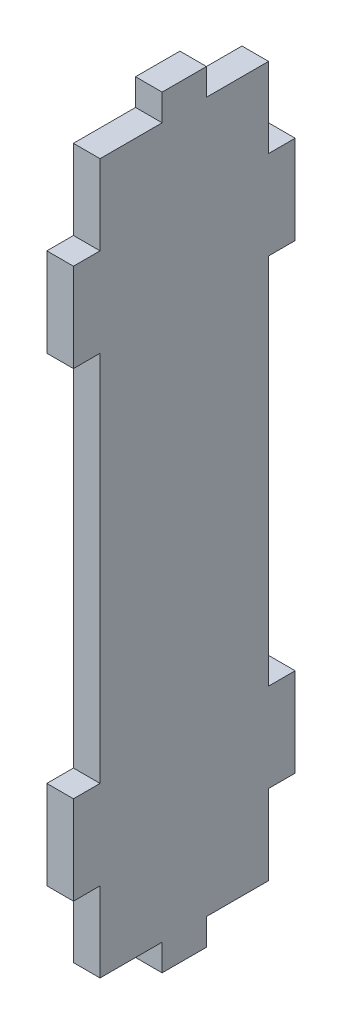
SolidWorks part; units mm, degrees
ref_plane "정면" through (0, 0, 0) normal (0, 0, 1) x (1, 0, 0)
ref_plane "윗면" through (0, 0, 0) normal (0, 1, 0) x (1, 0, 0)
ref_plane "우측면" through (0, 0, 0) normal (1, 0, 0) x (0, 0, -1)
sketch "스케치1" plane through (0, 0, 0) normal (1, 0, 0) x (0, 0, -1)
  line L1 (0, 0) -> (25, 0)
  line L2 (0, 0) -> (0, 86)
  line L3 (0, 86) -> (25, 86)
  line L4 (25, 0) -> (25, 86)
  dimension "D1" = 25
  dimension "D2" = 86
extrude "보스-돌출2" add sketch "스케치1" along normal blind 3
sketch "스케치4" plane through (3, 0, 0) normal (1, 0, 0) x (0, 0, -1)
  line L0 (-15.7111, 43) -> (42.1381, 43) construction
  line L1 (0, 86) -> (3, 86)
  line L2 (0, 86) -> (0, 74)
  line L3 (0, 74) -> (3, 74)
  line L4 (3, 86) -> (3, 74)
  line L5 (12.5, 89.488) -> (12.5, -3.3782) construction
  line L6 (25, 74) -> (22, 74)
  line L7 (22, 86) -> (22, 74)
  line L8 (25, 86) -> (22, 86)
  line L9 (25, 86) -> (25, 74)
  line L10 (25, 0) -> (25, 12)
  line L11 (25, 0) -> (22, 0)
  line L12 (22, 0) -> (22, 12)
  line L13 (25, 12) -> (22, 12)
  line L14 (0, 12) -> (3, 12)
  line L15 (3, 0) -> (3, 12)
  line L16 (0, 0) -> (3, 0)
  line L17 (0, 0) -> (0, 12)
  line L18 (0, 86) -> (0, 0) construction
  line L19 (0, 64) -> (3, 64)
  line L20 (0, 64) -> (0, 22)
  line L21 (0, 22) -> (3, 22)
  line L22 (3, 64) -> (3, 22)
  line L23 (25, 22) -> (22, 22)
  line L24 (22, 64) -> (22, 22)
  line L25 (25, 64) -> (22, 64)
  line L26 (25, 64) -> (25, 22)
  dimension "D1" = 12
  dimension "D2" = 3
  dimension "D3" = 10
  dimension "D4" = 10
extrude "컷-돌출1" cut sketch "스케치4" against normal through all
sketch "스케치5" plane through (3, 0, 0) normal (1, 0, 0) x (0, 0, -1)
  line L0 (22, 86) -> (22, 74) construction
  line L1 (3, 86) -> (22, 86)
  line L2 (3, 86) -> (3, 83)
  line L3 (3, 83) -> (10, 83)
  line L4 (22, 86) -> (22, 83)
  line L5 (15, 83) -> (22, 83)
  line L6 (10, 86) -> (15, 86)
  line L7 (10, 86) -> (10, 83)
  line L9 (15, 86) -> (15, 83)
  line L10 (-5.2829, 43) -> (29.4047, 43) construction
  line L11 (10, 0) -> (10, 3)
  line L12 (3, 0) -> (3, 3)
  line L13 (3, 3) -> (10, 3)
  line L14 (15, 0) -> (15, 3)
  line L15 (3, 0) -> (22, 0)
  line L16 (22, 0) -> (22, 3)
  line L17 (15, 3) -> (22, 3)
  line M13 (22, 74) -> (22, 86)
  line M14 (22, 86) -> (3, 86)
  line M15 (3, 86) -> (3, 74)
  line M23 (3, 12) -> (3, 0)
  line M24 (3, 0) -> (22, 0)
  line M25 (22, 0) -> (22, 12)
  dimension "D1" = 3
  dimension "D2" = 5
  dimension "D3" = 7
extrude "컷-돌출2" cut sketch "스케치5" against normal through all contours L7 L3 M14 M15 | L9 L5 M14 M13 | L13 L11 M23 M24 | L17 L14 M24 M25
